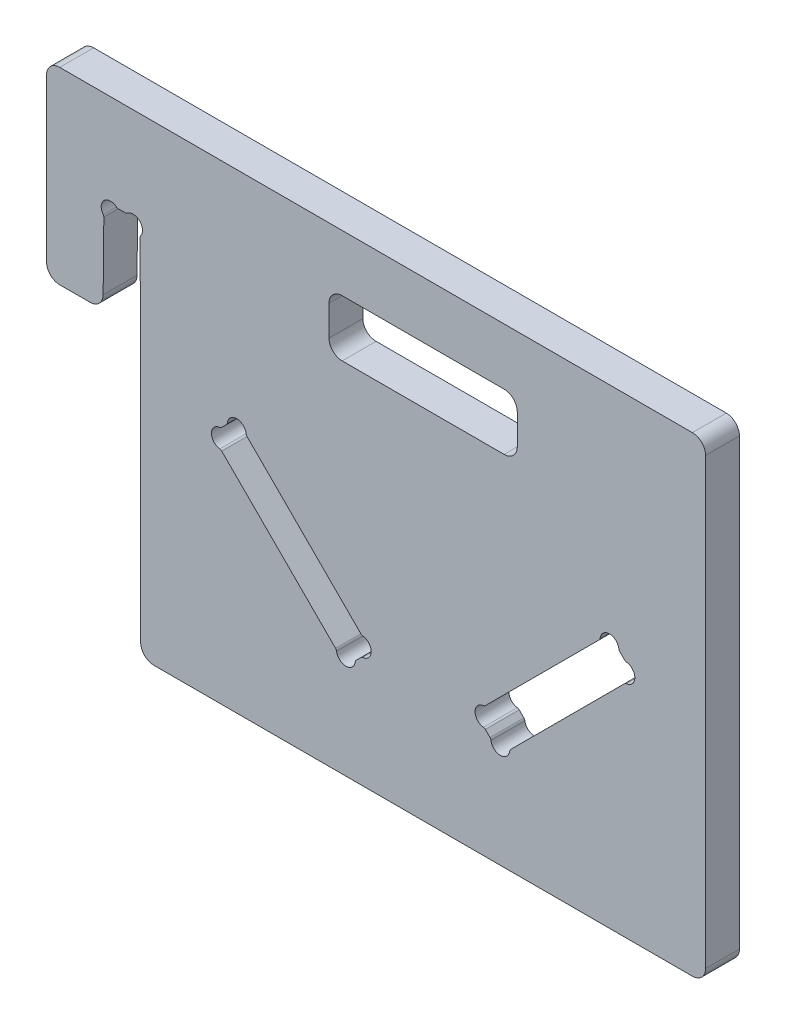
SolidWorks part; units mm, degrees
ref_plane "Plan de face" through (0, 0, 0) normal (0, 0, 1) x (1, 0, 0)
ref_plane "Plan de dessus" through (0, 0, 0) normal (0, 1, 0) x (1, 0, 0)
ref_plane "Plan de droite" through (0, 0, 0) normal (1, 0, 0) x (0, 0, -1)
sketch "Esquisse2" plane through (0, 0, 0) normal (0, 0, 1) x (1, 0, 0)
  line L0 (0, 0) -> (350, 0)
  line L2 (350, 0) -> (350, -250)
  line L3 (350, -250) -> (50, -250)
  line L4 (50, -250) -> (50, -100)
  line L5 (50, -100) -> (0, -100)
  line L6 (0, -100) -> (0, 0)
  dimension "D1" = 350
  dimension "D2" = 250
  dimension "D3" = 50
  dimension "D4" = 150
extrude "Boss.-Extru.2" add sketch "Esquisse2" along normal blind 18
sketch "Esquisse1" plane through (0, 0, 0) normal (0, 0, 1) x (1, 0, 0)
  line L0 (50, -250) -> (350, -250) construction
  line L1 (106.4896, -120.0545) -> (166.9455, -180.5104)
  line L2 (350, 0) -> (0, 0) construction
  line L3 (0, -100) -> (50, -100) construction
  line L4 (50, -100) -> (30, -100)
  line L5 (150, -30) -> (250, -30)
  line L6 (150, -30) -> (150, -60)
  line L7 (150, -60) -> (250, -60)
  line L8 (250, -30) -> (250, -60)
  line L9 (49.576, -57.1712) -> (50, -100)
  line L10 (49.5, -49.5) -> (49.5, -100) construction
  line L11 (93.0545, -133.4896) -> (153.5104, -193.9455)
  line L12 (30.424, -57.1712) -> (30, -100)
  line L13 (166.9455, -191.4723) -> (164.4723, -193.9455)
  line L14 (40, -49.5) -> (40, -100) construction
  line L15 (304.4723, -120.0545) -> (306.9455, -122.5277)
  line L16 (306.9455, -133.4896) -> (246.4896, -193.9455)
  line L17 (233.0545, -191.4723) -> (235.5277, -193.9455)
  line L18 (293.5104, -120.0545) -> (233.0545, -180.5104)
  line L19 (49.5, -49.5) -> (40, -59) construction
  line L20 (41.7488, -49.5) -> (38.2512, -49.5)
  line L24 (200, -227) -> (94.2911, -121.2911) construction
  line L26 (101.0086, -114.5736) -> (101.0086, -128.0086) construction
  line L29 (95.5277, -120.0545) -> (93.0545, -122.5277)
  line L30 (136.7175, -150.2825) -> (130, -157) construction
  line L31 (200, -250) -> (200, 0) construction
  arc A0 (49.9434, -56.0634) -> (49.576, -57.1712) centre (51.3759, -57.1534) ccw
  arc A1 (42.8647, -49.1123) -> (41.7488, -49.5) centre (41.7488, -47.7) cw
  arc A2 (30.0566, -56.0634) -> (30.424, -57.1712) centre (28.6241, -57.1534) cw
  arc A3 (30.0566, -56.0634) -> (37.1353, -49.1123) centre (34.0355, -53.0355) cw
  arc A4 (37.1353, -49.1123) -> (38.2512, -49.5) centre (38.2512, -47.7) ccw
  arc A5 (95.5277, -120.0545) -> (96.0426, -118.9914) centre (94.2549, -118.7817) ccw
  arc A6 (49.9434, -56.0634) -> (42.8647, -49.1123) centre (45.9645, -53.0355) ccw
  arc A7 (106.4896, -120.0545) -> (105.9746, -118.9914) centre (107.7624, -118.7817) cw
  arc A8 (105.9746, -118.9914) -> (96.0426, -118.9914) centre (101.0086, -119.5736) ccw
  arc A9 (93.0545, -133.4896) -> (91.9914, -132.9746) centre (91.7817, -134.7624) ccw
  arc A10 (91.9914, -132.9746) -> (91.9914, -123.0426) centre (92.5736, -128.0086) cw
  arc A11 (93.0545, -122.5277) -> (91.9914, -123.0426) centre (91.7817, -121.2549) cw
  arc A12 (153.5104, -193.9455) -> (154.0254, -195.0086) centre (152.2376, -195.2183) cw
  arc A13 (154.0254, -195.0086) -> (163.9574, -195.0086) centre (158.9914, -194.4264) ccw
  arc A14 (164.4723, -193.9455) -> (163.9574, -195.0086) centre (165.7451, -195.2183) ccw
  arc A15 (166.9455, -191.4723) -> (168.0086, -190.9574) centre (168.2183, -192.7451) cw
  arc A16 (168.0086, -181.0254) -> (168.0086, -190.9574) centre (167.4264, -185.9914) cw
  arc A17 (166.9455, -180.5104) -> (168.0086, -181.0254) centre (168.2183, -179.2376) ccw
  arc A18 (293.5104, -120.0545) -> (294.0254, -118.9914) centre (292.2376, -118.7817) ccw
  arc A19 (294.0254, -118.9914) -> (303.9574, -118.9914) centre (298.9914, -119.5736) cw
  arc A20 (304.4723, -120.0545) -> (303.9574, -118.9914) centre (305.7451, -118.7817) cw
  arc A21 (306.9455, -122.5277) -> (308.0086, -123.0426) centre (308.2183, -121.2549) ccw
  arc A22 (308.0086, -132.9746) -> (308.0086, -123.0426) centre (307.4264, -128.0086) ccw
  arc A23 (306.9455, -133.4896) -> (308.0086, -132.9746) centre (308.2183, -134.7624) cw
  arc A24 (246.4896, -193.9455) -> (245.9746, -195.0086) centre (247.7624, -195.2183) ccw
  arc A25 (245.9746, -195.0086) -> (236.0426, -195.0086) centre (241.0086, -194.4264) cw
  arc A26 (235.5277, -193.9455) -> (236.0426, -195.0086) centre (234.2549, -195.2183) cw
  arc A27 (233.0545, -191.4723) -> (231.9914, -190.9574) centre (231.7817, -192.7451) ccw
  arc A28 (231.9914, -181.0254) -> (231.9914, -190.9574) centre (232.5736, -185.9914) ccw
  arc A29 (233.0545, -180.5104) -> (231.9914, -181.0254) centre (231.7817, -179.2376) cw
  point P8 (200, -30)
  point P14 (200, -250)
  point P51 (123.2825, -163.7175)
  point P58 (94.2911, -121.2911)
  point P65 (130, -157)
  dimension "D5" = 5
  dimension "D11" = 5
  dimension "D8" = 1.8
  dimension "D18" = 1.8
  dimension "D2" = 45
  dimension "D9" = 45
  dimension "D12" = 50.5
  dimension "D13" = 50.5
  dimension "D3" = 100
  dimension "D6" = 30
  dimension "D16" = 70
  dimension "D7" = 30
  dimension "D4" = 9.5
  dimension "D17" = 0.5
  dimension "D14" = 23
  dimension "D15" = 45
  dimension "D10" = 9.5
extrude "Enlèv. mat.-Extru.1" cut sketch "Esquisse1" along normal through all
fillet "Congé1" radius 7 10 edges at (350, 0, 9) (350, -250, 9) (50, -250, 9) (0, -100, 9) (0, 0, 9) (250, -30, 9) (250, -60, 9) (150, -60, 9) (150, -30, 9) (30, -100, 9)
equation "\"D1@Boss.-Extru.2\" = \"material_thickness\""
equation "\"D4@Esquisse1\" = \"material_thickness\" / 2 + \"clearance\""
equation "\"D10@Esquisse1\"= \"material_thickness\" / 2 + \"clearance\""
equation "\"D11@Esquisse1\"=\"tool_diameter\"/2+\"hole_clearance\""
equation "\"D5@Esquisse1\"=\"tool_diameter\"/2+\"hole_clearance\""
equation "\"D1@Congé1\"=\"fillet\""
equation "\"D12@Esquisse1\"=50+\"clearance\""
equation "\"D13@Esquisse1\"=50+\"clearance\""
equation "\"D8@Esquisse1\"=\"material_thickness\"/10"
equation "\"tool_diameter\"=9"
equation "\"hole_clearance\"=0.5"
equation "\"material_thickness\"=18"
equation "\"clearance\"=0.5"
equation "\"outer_slot\"=0.5"
equation "\"fillet\"=7"
equation "\"D17@Esquisse1\"=\"outer_slot\""
equation "\"D18@Esquisse1\"=\"material_thickness\"/10"
equation "\"string\"= 2 * \"tool_diameter\" / 2 * cos ( 45deg )"
equation "\"angle\"= IIF ( \"string\" < \"limit\" , 45 , ( 180 - 2 * arcsin ( \"ThicknessVStool_dia\" ) ) / 2 )"
equation "\"limit\"= \"material_thickness\" / 2 * 9 / 10"
equation "\"ThicknessVStool_dia\"= IIF ( \"limit\" / \"tool_diameter\" > 1 , 1 , \"limit\" / \"tool_diameter\" )"
equation "\"D9@Esquisse1\"=\"angle\""
equation "\"D2@Esquisse1\"=\"angle\""
